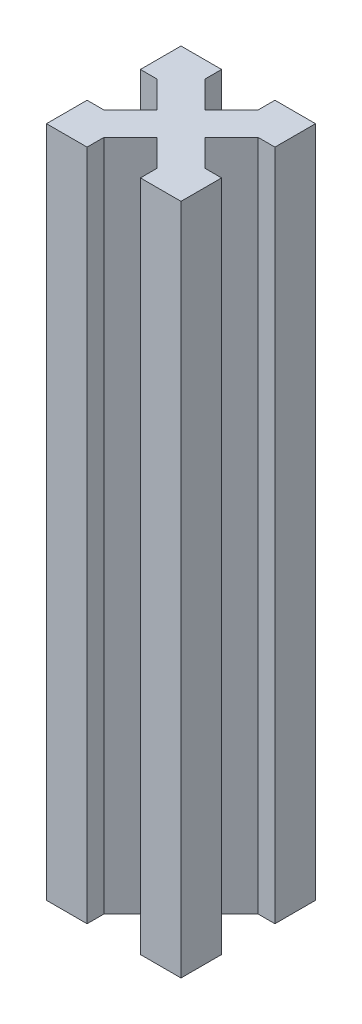
SolidWorks part; units mm, degrees
ref_plane "Plan de face" through (0, 0, 0) normal (0, 0, 1) x (1, 0, 0)
ref_plane "Plan de dessus" through (0, 0, 0) normal (0, 1, 0) x (1, 0, 0)
ref_plane "Plan de droite" through (0, 0, 0) normal (1, 0, 0) x (0, 0, -1)
sketch "Esquisse1" plane through (0, 0, 0) normal (0, 1, 0) x (1, 0, 0)
  line L0 (-2.5, 17.5) -> (-17.5, 17.5)
  line L1 (0, 0) -> (-20, 0)
  line L2 (0, 0) -> (0, 20)
  line L3 (0, 20) -> (-20, 20)
  line L4 (-20, 0) -> (-20, 20)
  line L5 (0, 20) -> (-20, 0) construction
  line L6 (-17.5, 2.5) -> (-17.5, 17.5)
  line L11 (-2.5, 2.5) -> (-17.5, 2.5)
  line L12 (-2.5, 2.5) -> (-2.5, 17.5)
  line L13 (-20, 20) -> (0, 0) construction
  line L14 (-26.9957, 23.4601) -> (-23.4601, 26.9957)
  line L15 (-26.9957, 23.4601) -> (3.4601, -6.9957)
  line L16 (-23.4601, 26.9957) -> (6.9957, -3.4601)
  line L17 (3.4601, -6.9957) -> (6.9957, -3.4601)
  line L18 (-26.9957, 23.4601) -> (6.9957, -3.4601) construction
  line L19 (-23.4601, 26.9957) -> (3.4601, -6.9957) construction
  line L20 (-10, 20) -> (-10, 0) construction
  line L21 (-23.4601, -6.9957) -> (-26.9957, -3.4601)
  line L22 (3.4601, 26.9957) -> (-26.9957, -3.4601)
  line L23 (6.9957, 23.4601) -> (-23.4601, -6.9957)
  line L24 (6.9957, 23.4601) -> (3.4601, 26.9957)
  line L25 (-17.5, 13.9645) -> (-20, 13.9645)
  line L26 (-20, 10) -> (0, 10) construction
  line L27 (-17.5, 6.0355) -> (-20, 6.0355)
  line L28 (-2.5, 6.0355) -> (0, 6.0355)
  line L29 (-2.5, 13.9645) -> (0, 13.9645)
  line L30 (-2.5, 6.0355) -> (0, 6.0355)
  line L31 (-2.5, 13.9645) -> (0, 13.9645)
  line L32 (-13.9645, 2.5) -> (-13.9645, 0)
  line L33 (-6.0355, 17.5) -> (-6.0355, 20)
  line L34 (-13.9645, 17.5) -> (-13.9645, 20)
  line L35 (-6.0355, 2.5) -> (-6.0355, 0)
  point P11 (-10, 10)
  dimension "D1" = 20
  dimension "D2" = 20
  dimension "D3" = 7.3934
  dimension "D4" = 2.5
  dimension "D5" = 43.071
  dimension "D6" = 2.5
extrude "Boss.-Extru.1" add sketch "Esquisse1" along normal blind 100 contours L15 L35 L1 | L16 L12 L11 L15 L1 L2 | L28 L16 L2 | L16 L23 L15 L11 L12 | L32 L23 L1 | L23 L11 L6 L22 L4 L1 | L22 L27 L4 | L23 L15 L22 L6 L11 | L23 L16 L22 L15 | L23 L12 L0 L22 L16 | L23 L2 L3 L22 L0 L12 | L23 L29 L2 | L33 L22 L3 | L16 L34 L3 | L16 L3 L4 L15 L6 L0 | L25 L15 L4 | L22 L16 L0 L6 L15
